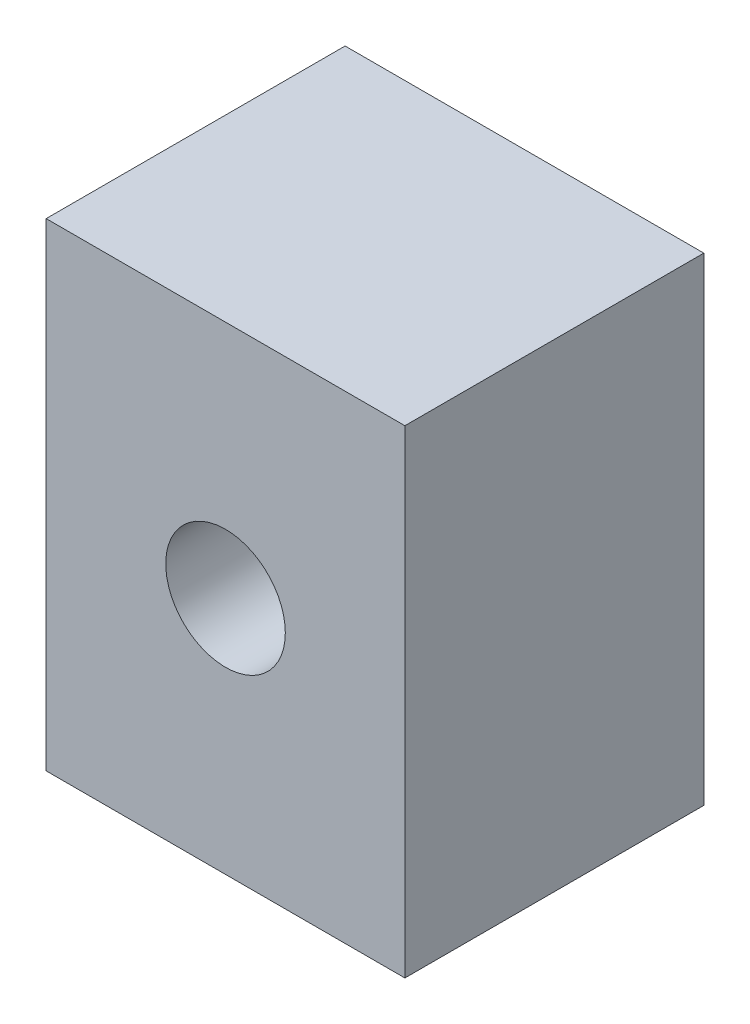
SolidWorks part; units mm, degrees
material "1023 Carbon Steel Sheet (SS)"
ref_plane "Front Plane" through (0, 0, 0) normal (0, 0, 1) x (1, 0, 0)
ref_plane "Top Plane" through (0, 0, 0) normal (0, 1, 0) x (1, 0, 0)
ref_plane "Right Plane" through (0, 0, 0) normal (1, 0, 0) x (0, 0, -1)
sketch "Sketch1" plane through (0, 0, 0) normal (0, 1, 0) x (1, 0, 0)
  line L1 (-15, -12.5) -> (15, -12.5)
  line L2 (-15, -12.5) -> (-15, 12.5)
  line L3 (-15, 12.5) -> (15, 12.5)
  line L4 (15, -12.5) -> (15, 12.5)
  line L5 (-15, -12.5) -> (15, 12.5) construction
  line L6 (-15, 12.5) -> (15, -12.5) construction
  point P0 (0, 0)
extrude "Boss-Extrude1" add sketch "Sketch1" along normal blind 40
sketch "Sketch2" plane through (0, 0, 12.5) normal (0, 0, 1) x (1, 0, 0)
  line L0 (-15, 0) -> (15, 0) construction
  line L2 (-15, 40) -> (-15, 0) construction
  circle A0 centre (0, 20) radius 5
  point P6 (15, 26.1888)
  dimension "D1" = 20
  dimension "D2" = 15
extrude "Cut-Extrude1" cut sketch "Sketch2" against normal blind 40
